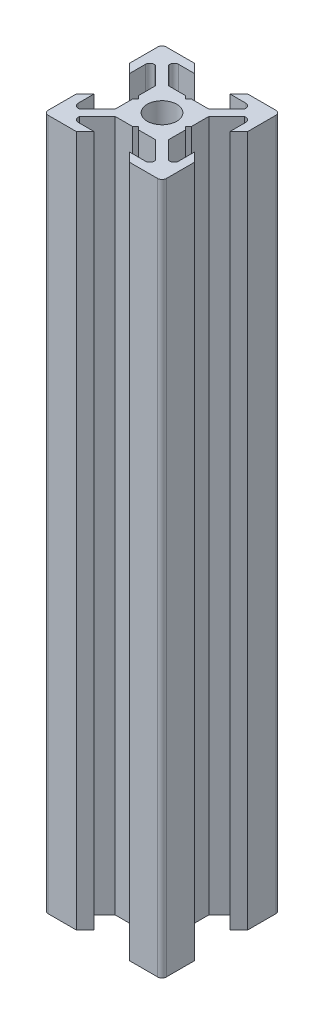
SolidWorks part; units mm, degrees
ref_plane "Face" through (0, 0, 0) normal (0, 0, 1) x (1, 0, 0)
ref_plane "Dessus" through (0, 0, 0) normal (0, 1, 0) x (1, 0, 0)
ref_plane "Droite" through (0, 0, 0) normal (1, 0, 0) x (0, 0, -1)
sketch "Esquisse1" plane through (0, 0, 0) normal (0, 1, 0) x (1, 0, 0)
  line L0 (0, 0) -> (0, 10) construction
  line L1 (0, 0) -> (-10, 0) construction
  line L2 (-10, 0) -> (-10, 10) construction
  line L3 (-10, 10) -> (0, 10) construction
  line L4 (0, 4) -> (-0.5, 4.5)
  line L5 (-0.5, 4.5) -> (-3.4393, 4.5)
  line L6 (-3.4393, 4.5) -> (-6.4393, 7.5)
  line L7 (-6.4393, 7.5) -> (-6.4393, 8.5)
  line L8 (-6.4393, 8.5) -> (-3, 8.5)
  line L9 (-3, 8.5) -> (-4.5, 10)
  line L10 (-4.5, 10) -> (-10, 10)
  line L11 (0, 0) -> (-10, 10) construction
  line L12 (-10, 4.5) -> (-10, 10)
  line L13 (-8.5, 3) -> (-10, 4.5)
  line L14 (-8.5, 6.4393) -> (-8.5, 3)
  line L15 (-7.5, 6.4393) -> (-8.5, 6.4393)
  line L16 (-4.5, 3.4393) -> (-7.5, 6.4393)
  line L17 (-4.5, 0.5) -> (-4.5, 3.4393)
  line L18 (-4, 0) -> (-4.5, 0.5)
  line L19 (0, -4) -> (-0.5, -4.5)
  line L20 (-0.5, -4.5) -> (-3.4393, -4.5)
  line L21 (-4, 0) -> (-4.5, -0.5)
  line L22 (-4.5, -0.5) -> (-4.5, -3.4393)
  line L23 (-4.5, -3.4393) -> (-7.5, -6.4393)
  line L24 (-3.4393, -4.5) -> (-6.4393, -7.5)
  line L25 (-3, -8.5) -> (-4.5, -10)
  line L26 (-6.4393, -8.5) -> (-3, -8.5)
  line L27 (-6.4393, -7.5) -> (-6.4393, -8.5)
  line L28 (-7.5, -6.4393) -> (-8.5, -6.4393)
  line L29 (-4.5, -10) -> (-10, -10)
  line L30 (-10, -4.5) -> (-10, -10)
  line L31 (-8.5, -3) -> (-10, -4.5)
  line L32 (-8.5, -6.4393) -> (-8.5, -3)
  line L33 (8.5, -6.4393) -> (8.5, -3)
  line L34 (8.5, -3) -> (10, -4.5)
  line L35 (10, -4.5) -> (10, -10)
  line L36 (4.5, -10) -> (10, -10)
  line L37 (7.5, -6.4393) -> (8.5, -6.4393)
  line L38 (6.4393, -7.5) -> (6.4393, -8.5)
  line L39 (6.4393, -8.5) -> (3, -8.5)
  line L40 (3, -8.5) -> (4.5, -10)
  line L41 (3.4393, -4.5) -> (6.4393, -7.5)
  line L42 (4.5, -3.4393) -> (7.5, -6.4393)
  line L43 (4.5, -0.5) -> (4.5, -3.4393)
  line L44 (4, 0) -> (4.5, -0.5)
  line L45 (0.5, -4.5) -> (3.4393, -4.5)
  line L46 (0, -4) -> (0.5, -4.5)
  line L47 (4, 0) -> (4.5, 0.5)
  line L48 (4.5, 0.5) -> (4.5, 3.4393)
  line L49 (4.5, 3.4393) -> (7.5, 6.4393)
  line L50 (7.5, 6.4393) -> (8.5, 6.4393)
  line L51 (8.5, 6.4393) -> (8.5, 3)
  line L52 (8.5, 3) -> (10, 4.5)
  line L53 (10, 4.5) -> (10, 10)
  line L54 (4.5, 10) -> (10, 10)
  line L55 (3, 8.5) -> (4.5, 10)
  line L56 (6.4393, 8.5) -> (3, 8.5)
  line L57 (6.4393, 7.5) -> (6.4393, 8.5)
  line L58 (3.4393, 4.5) -> (6.4393, 7.5)
  line L59 (0.5, 4.5) -> (3.4393, 4.5)
  line L60 (0, 4) -> (0.5, 4.5)
  circle A0 centre (0, 0) radius 2.5
  dimension "D10" = 5
  dimension "D1" = 10
  dimension "D2" = 45
  dimension "D3" = 45
  dimension "D4" = 1.5
  dimension "D5" = 7
  dimension "D6" = 1
  dimension "D7" = 4.5
  dimension "D8" = 0.5
  dimension "D9" = 0.75
extrude "Extrusion1" add sketch "Esquisse1" along normal blind 117
fillet "Congé1" radius 0.75 12 edges at (-8.5, 58.5, -6.4393) (-6.4393, 58.5, -8.5) (8.5, 58.5, -6.4393) (6.4393, 58.5, -8.5) (-8.5, 58.5, 6.4393) (-6.4393, 58.5, 8.5) (8.5, 58.5, 6.4393) (6.4393, 58.5, 8.5) (10, 58.5, -10) (-10, 58.5, -10) (-10, 58.5, 10) (10, 58.5, 10)
